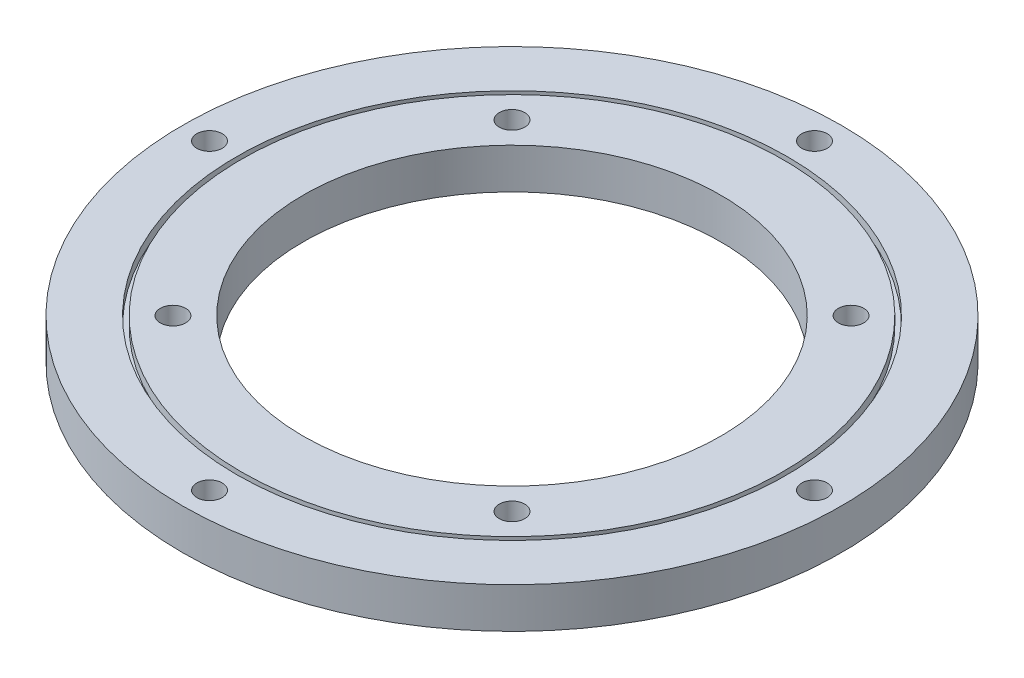
SolidWorks part; units mm, degrees
ref_plane "Front Plane" through (0, 0, 0) normal (0, 0, 1) x (1, 0, 0)
ref_plane "Top Plane" through (0, 0, 0) normal (0, 1, 0) x (1, 0, 0)
ref_plane "Right Plane" through (0, 0, 0) normal (1, 0, 0) x (0, 0, -1)
sketch "Sketch1" plane through (0, 0, 0) normal (0, 1, 0) x (1, 0, 0)
  circle A0 centre (0, 0) radius 70
  circle A1 centre (0, 0) radius 44.35
  dimension "D1" = 140
  dimension "D2" = 88.7
extrude "Boss-Extrude1" add sketch "Sketch1" along normal blind 8.6
sketch "Sketch2" plane through (0, 8.6, 0) normal (0, 1, 0) x (1, 0, 0)
  circle A0 centre (0, 0) radius 70 construction
  circle A1 centre (0, 0) radius 58 construction
  circle A2 centre (0, 0) radius 70 construction
  circle A3 centre (0, 0) radius 58.5
  circle A4 centre (0, 0) radius 57.5
  dimension "D1" = 12
  dimension "D2" = 0.5
  dimension "D3" = 0.5
extrude "Cut-Extrude1" cut sketch "Sketch2" against normal blind 2
ref_plane "Plane1" through (0, 4.3, 0) normal (0, 1, 0) x (1, 0, 0)
mirror "Mirror1" about plane through (0, 4.3, 0) normal (0, 1, 0) of "Cut-Extrude1"
sketch "Sketch3" plane through (0, 8.6, 0) normal (0, 1, 0) x (1, 0, 0)
  line L0 (0, 70) -> (0, 58.5) construction
  circle A0 centre (0, 0) radius 70 construction
  circle A1 centre (0, 0) radius 58.5 construction
  circle A2 centre (0, 0) radius 58.5 construction
  circle A3 centre (0, 64.25) radius 2.7
  circle A4 centre (64.25, 0) radius 2.7
  circle A5 centre (0, -64.25) radius 2.7
  circle A6 centre (-64.25, 0) radius 2.7
  point P20 (0, 0)
  dimension "D1" = 5.4
  dimension "D2" = 4
extrude "Cut-Extrude2" cut sketch "Sketch3" against normal through all
sketch "Sketch4" plane through (0, 8.6, 0) normal (0, 1, 0) x (1, 0, 0)
  line L0 (0, 0) -> (-31.3602, 31.3602) construction
  line L1 (-31.3602, 31.3602) -> (-40.6586, 40.6586) construction
  line L2 (0, 0) -> (0, 44.35) construction
  circle A0 centre (0, 0) radius 44.35 construction
  circle A1 centre (0, 0) radius 57.5 construction
  circle A2 centre (-36.0094, 36.0094) radius 2.7
  circle A3 centre (36.0094, 36.0094) radius 2.7
  circle A4 centre (36.0094, -36.0094) radius 2.7
  circle A5 centre (-36.0094, -36.0094) radius 2.7
  point P21 (0, 0)
  dimension "D2" = 5.4
  dimension "D1" = 45
  dimension "D3" = 4
extrude "Cut-Extrude3" cut sketch "Sketch4" against normal through all
